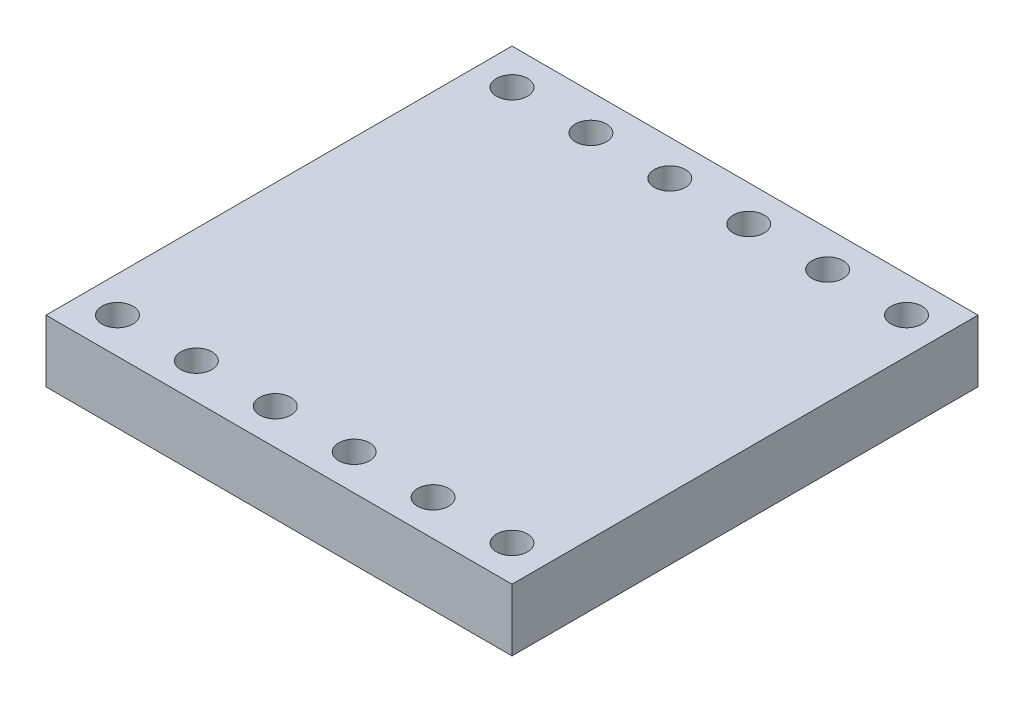
SolidWorks part; units mm, degrees
ref_plane "Front Plane" through (0, 0, 0) normal (0, 0, 1) x (1, 0, 0)
ref_plane "Top Plane" through (0, 0, 0) normal (0, 1, 0) x (1, 0, 0)
ref_plane "Right Plane" through (0, 0, 0) normal (1, 0, 0) x (0, 0, -1)
sketch "Sketch1" plane through (0, 0, 0) normal (0, 1, 0) x (1, 0, 0)
  line L1 (0, 0) -> (15, 0)
  line L2 (0, 0) -> (0, 15)
  line L3 (0, 15) -> (15, 15)
  line L4 (15, 0) -> (15, 15)
  dimension "D1" = 15
  dimension "D2" = 15
extrude "Boss-Extrude1" add sketch "Sketch1" along normal blind 2
sketch "Sketch3" plane through (0, 2, 0) normal (0, 1, 0) x (1, 0, 0)
  line L0 (0, 0) -> (15, 0) construction
  line L1 (15, 0) -> (15, 15) construction
  circle A0 centre (13.85, 1.15) radius 0.5
  circle A1 centre (11.31, 1.15) radius 0.5
  circle A2 centre (8.77, 1.15) radius 0.5
  circle A3 centre (6.23, 1.15) radius 0.5
  circle A4 centre (3.69, 1.15) radius 0.5
  circle A5 centre (1.15, 1.15) radius 0.5
  circle A6 centre (13.85, 13.85) radius 0.5
  circle A7 centre (11.31, 13.85) radius 0.5
  circle A8 centre (8.77, 13.85) radius 0.5
  circle A9 centre (6.23, 13.85) radius 0.5
  circle A10 centre (3.69, 13.85) radius 0.5
  circle A11 centre (1.15, 13.85) radius 0.5
  dimension "D1" = 1
  dimension "D3" = 2.54
  dimension "D5" = 12.7
  dimension "D6" = 1.15
  dimension "D7" = 1.15
  dimension "D2" = 6
  dimension "D4" = 2
extrude "Cut-Extrude1" cut sketch "Sketch3" against normal up to surface (2 mm away) up to face at (7.5, 0, -7.5)
